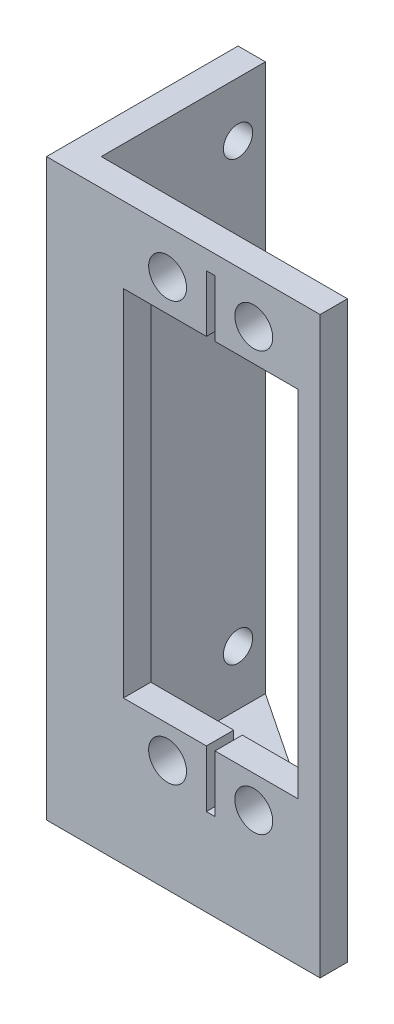
SolidWorks part; units mm, degrees
ref_plane "Front Plane" through (0, 0, 0) normal (0, 0, 1) x (1, 0, 0)
ref_plane "Top Plane" through (0, 0, 0) normal (0, 1, 0) x (1, 0, 0)
ref_plane "Right Plane" through (0, 0, 0) normal (1, 0, 0) x (0, 0, -1)
sketch "Sketch2" plane through (0, 0, 0) normal (0, 0, 1) x (1, 0, 0)
  line L1 (0, 0) -> (31.75, 0)
  line L2 (0, 0) -> (0, 63.5)
  line L3 (0, 63.5) -> (31.75, 63.5)
  line L4 (31.75, 0) -> (31.75, 63.5)
  dimension "D1" = 63.5
  dimension "D2" = 31.75
extrude "Boss-Extrude1" add sketch "Sketch2" along normal blind 3.175 contours L4 L3 L2 L1
sketch "Sketch3" plane through (0, 0, 3.175) normal (0, 0, 1) x (1, 0, 0)
  line L0 (8.923, 54.704) -> (29.177, 13.55) construction
  line L1 (8.923, 54.704) -> (18.55, 54.704)
  line L2 (8.923, 54.704) -> (8.923, 13.55)
  line L3 (8.923, 13.55) -> (18.55, 13.55)
  line L4 (29.177, 54.704) -> (29.177, 13.55)
  line L5 (29.177, 54.704) -> (8.923, 13.55) construction
  line L6 (14.05, 58.427) -> (24.05, 9.827) construction
  line L7 (14.05, 9.827) -> (24.05, 58.427) construction
  line L8 (19.55, 13.55) -> (29.177, 13.55)
  line L9 (18.55, 13.55) -> (18.55, 6.946)
  line L10 (18.55, 6.946) -> (19.55, 6.946)
  line L11 (19.55, 13.55) -> (19.55, 6.946)
  line L12 (19.05, 34.127) -> (62.1329, 34.127) construction
  line L13 (18.55, 61.308) -> (19.55, 61.308)
  line L14 (18.55, 54.704) -> (18.55, 61.308)
  line L15 (19.55, 54.704) -> (19.55, 61.308)
  line L16 (19.55, 54.704) -> (29.177, 54.704)
  line L17 (0, 0) -> (0, 63.5) construction
  line L18 (0, 63.5) -> (31.75, 63.5) construction
  circle A0 centre (14.05, 9.827) radius 2.2
  circle A1 centre (24.05, 9.827) radius 2.2
  circle A2 centre (14.05, 58.427) radius 2.2
  circle A3 centre (24.05, 58.427) radius 2.2
  point P8 (19.05, 6.946)
  point P17 (19.05, 34.127)
  point P18 (19.05, 34.127)
  point P27 (19.05, 44.45)
  dimension "D3" = 4.4
  dimension "D1" = 10
  dimension "D2" = 48.6
  dimension "D4" = 41.154
  dimension "D5" = 20.254
  dimension "D6" = 1
  dimension "D7" = 6.604
  dimension "D8" = 30.9
  dimension "D9" = 19.05
  dimension "D10" = 19.05
extrude "Cut-Extrude1" cut sketch "Sketch3" against normal through all
sketch "Sketch4" plane through (0, 0, 3.175) normal (0, 0, 1) x (1, 0, 0)
  line L0 (0, 0) -> (31.75, 0) construction
  line L1 (0, 63.5) -> (3.175, 63.5)
  line L2 (0, 63.5) -> (0, 0)
  line L3 (0, 0) -> (3.175, 0)
  line L4 (3.175, 63.5) -> (3.175, 0)
  dimension "D1" = 3.175
extrude "Boss-Extrude2" add sketch "Sketch4" against normal blind 19.05 from surface at -3.175 starting at face at (26.25, 9.827, 0)
sketch "Sketch5" plane through (0, 0, 0) normal (0, -1, 0) x (1, 0, 0)
  line L0 (0, 3.175) -> (31.75, 3.175)
  line L1 (31.75, 3.175) -> (31.75, 0)
  line L2 (31.75, 0) -> (3.175, -19.05)
  line L3 (3.175, -19.05) -> (0, -19.05)
  line L4 (0, -19.05) -> (0, 3.175)
extrude "Boss-Extrude3" add sketch "Sketch5" along normal blind 3.175
sketch "Sketch6" plane through (3.175, 0, 0) normal (1, 0, 0) x (0, 0, -1)
  line L0 (0, 0) -> (0, 63.5) construction
  line L1 (19.05, 0) -> (19.05, 63.5) construction
  line L2 (19.05, 63.5) -> (0, 63.5) construction
  line L4 (19.05, 0) -> (0, 0) construction
  circle A0 centre (3.175, 57.15) radius 1.7
  circle A1 centre (3.175, 6.35) radius 1.7
  circle A2 centre (15.875, 57.15) radius 1.7
  circle A3 centre (15.875, 6.35) radius 1.7
  dimension "D5" = 3.4
  dimension "D1" = 3.175
  dimension "D2" = 3.175
  dimension "D3" = 6.35
  dimension "D4" = 6.35
extrude "Cut-Extrude2" cut sketch "Sketch6" against normal through all
sketch "Sketch7" plane through (0, 0, 3.175) normal (0, 0, 1) x (1, 0, 0)
  line L0 (18.55, 54.704) -> (8.923, 54.704) construction
  line L1 (8.923, 13.55) -> (18.55, 13.55) construction
  line L2 (19.55, 61.308) -> (18.55, 61.308) construction
  point P0 (19.05, 44.45)
  point P1 (19.05, 23.804)
  point P8 (19.05, 61.308)
  dimension "D1" = 30.9
  dimension "D2" = 30.9
equation "\"D8@Sketch3\"=30.9mm"
equation "\"tighttol\" = 0.005in"
equation "\"normtol\" = 0.01in"
equation "\"loosetol\" = 0.02in"
equation "\"D5@Sketch6\"=3.4mm"
equation "\"D3@Sketch3\"=4.4mm"
equation "\"D1@Sketch7\"=30.9mm"
equation "\"D2@Sketch7\"=30.9mm"
